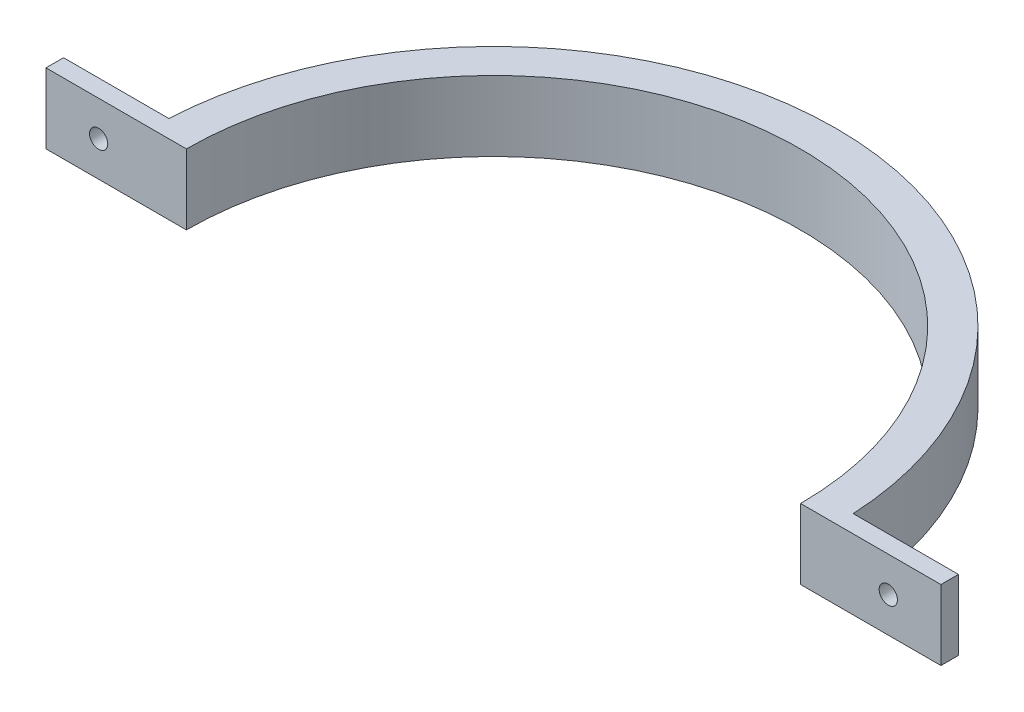
SolidWorks part; units mm, degrees
ref_plane "Front Plane" through (0, 0, 0) normal (0, 0, 1) x (1, 0, 0)
ref_plane "Top Plane" through (0, 0, 0) normal (0, 1, 0) x (1, 0, 0)
ref_plane "Right Plane" through (0, 0, 0) normal (1, 0, 0) x (0, 0, -1)
sketch "Sketch1" plane through (0, 0, 0) normal (0, 1, 0) x (1, 0, 0)
  line L0 (-55.5625, 0) -> (-80.9625, 0)
  line L1 (-80.9625, 0) -> (-80.9625, 3.175)
  line L2 (-80.9625, 3.175) -> (-61.9125, 3.175)
  line L3 (0, 0) -> (0, 89.1254) construction
  line L4 (80.9625, 3.175) -> (61.9125, 3.175)
  line L5 (80.9625, 0) -> (80.9625, 3.175)
  line L6 (55.5625, 0) -> (80.9625, 0)
  arc A0 (-55.5625, 0) -> (55.5625, 0) centre (0, 0) cw
  arc A1 (-61.9125, 3.175) -> (61.9125, 3.175) centre (0, 0) cw
  point P4 (0, 0)
  dimension "D1" = 55.5625
  dimension "D2" = 25.4
  dimension "D3" = 3.175
  dimension "D4" = 19.05
extrude "Boss-Extrude1" add sketch "Sketch1" along normal blind 12.7
sketch "Sketch5" plane through (0, 0, -3.175) normal (0, 0, -1) x (-1, 0, 0)
  line L0 (71.4375, 12.7) -> (71.4375, 0) construction
  line L1 (61.9125, 12.7) -> (80.9625, 12.7) construction
  line L2 (61.9125, 0) -> (80.9625, 0) construction
  circle A0 centre (71.4375, 6.35) radius 1.651
  dimension "D1" = 3.302
extrude "Cut-Extrude1" cut sketch "Sketch5" against normal through all
mirror "Mirror1" about plane through (0, 0, 0) normal (1, 0, 0) of "Cut-Extrude1"
